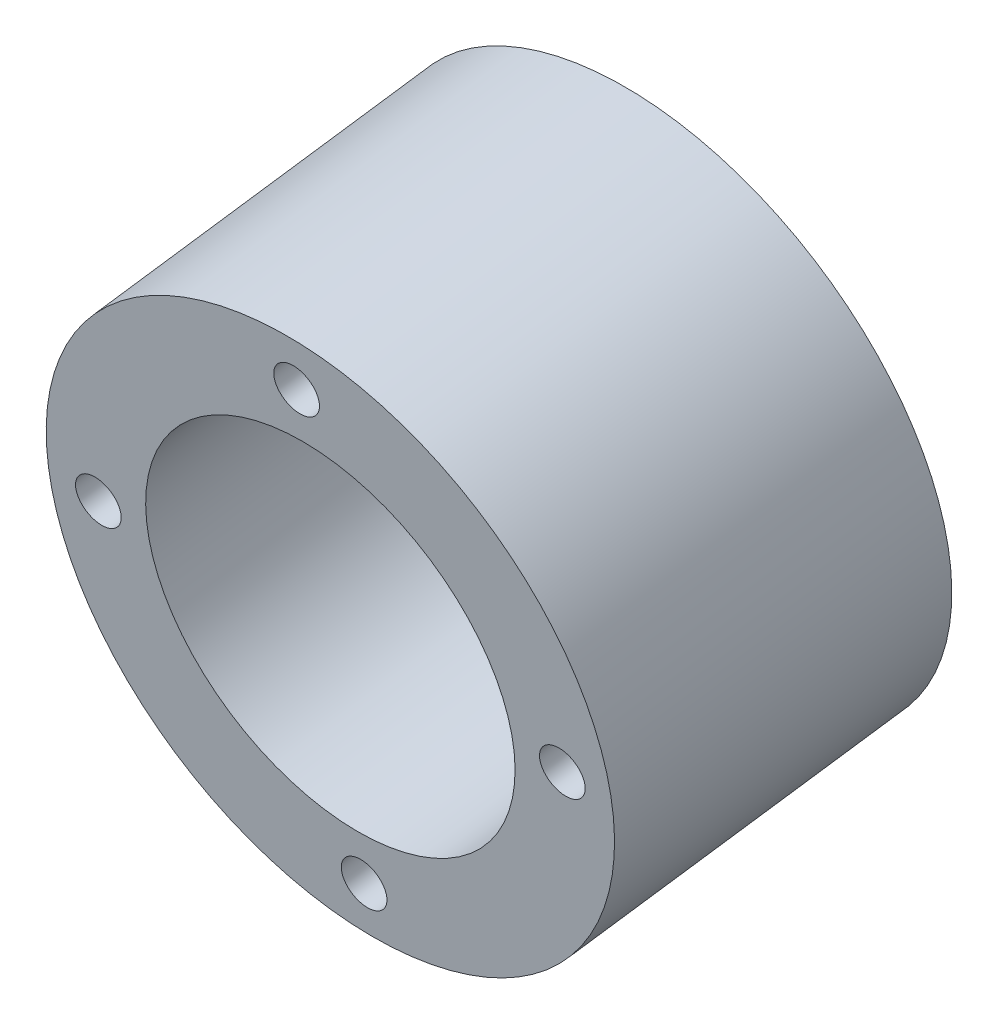
SolidWorks part; units mm, degrees
material "Cast Alloy Steel"
ref_plane "Front Plane" through (0, 0, 0) normal (0, 0, 1) x (1, 0, 0)
ref_plane "Top Plane" through (0, 0, 0) normal (0, 1, 0) x (1, 0, 0)
ref_plane "Right Plane" through (0, 0, 0) normal (1, 0, 0) x (0, 0, -1)
ref_plane "Plane1" through (0, 577.9269, 1367.6544) normal (-0.005, -0.1447, 0.9895) x (1, -0.0007, 0.005)
sketch "Sketch1" plane through (0, 577.9269, 1367.6544) normal (-0.005, -0.1447, 0.9895) x (1, -0.0007, 0.005)
  circle A0 centre (0, 0) radius 20.6375
  circle A1 centre (0, 0) radius 31.75
  point P9 (0, 26.1938)
  point P10 (-26.1938, 0)
  point P17 (0, -26.1938)
  point P18 (26.1938, 0)
  dimension "D1" = 63.5
  dimension "D2" = 41.275
extrude "Boss-Extrude1" add sketch "Sketch1" along normal mid plane 38.1
hole_wizard "1/4-20 Tapped Hole1" positions "Sketch5" profile "Sketch6" tap size "1/4-20" standard "ANSI Inch" end condition up to next
sketch "Sketch5" plane through (-6.2644, -180.94, 1237.4042) normal (0.005, 0.1447, -0.9895) x (-1, 0.001, -0.0049)
  point P0 (-32.3046, 769.7388)
  point P3 (-6.1014, 795.923)
  point P6 (20.0829, 769.7198)
  point P9 (-6.1203, 743.5356)
sketch "Sketch6" plane through (26.2888, 580.6652, 1348.9351) normal (0.7031, 0.7031, 0.1064) x (-0.7111, 0.6962, 0.0982)
  line L0 (0, 0) -> (0, 38.1)
  line L1 (0, 38.1) -> (2.5527, 38.1)
  line L2 (2.5527, 38.1) -> (2.5527, 0)
  line L5 (2.5527, 0) -> (0, 0)
  line L11 (0, -6.35) -> (0, 107.95) construction
  dimension "Thru Tap Drill Dia." = 5.1054
  dimension "Thru Tap Drill Depth" = 38.1
cosmetic thread "Hole Thread5" parameters "D2"=6.35
cosmetic thread "Hole Thread6" parameters "D2"=6.35
cosmetic thread "Hole Thread7" parameters "D2"=6.35
cosmetic thread "Hole Thread8" parameters "D2"=6.35
